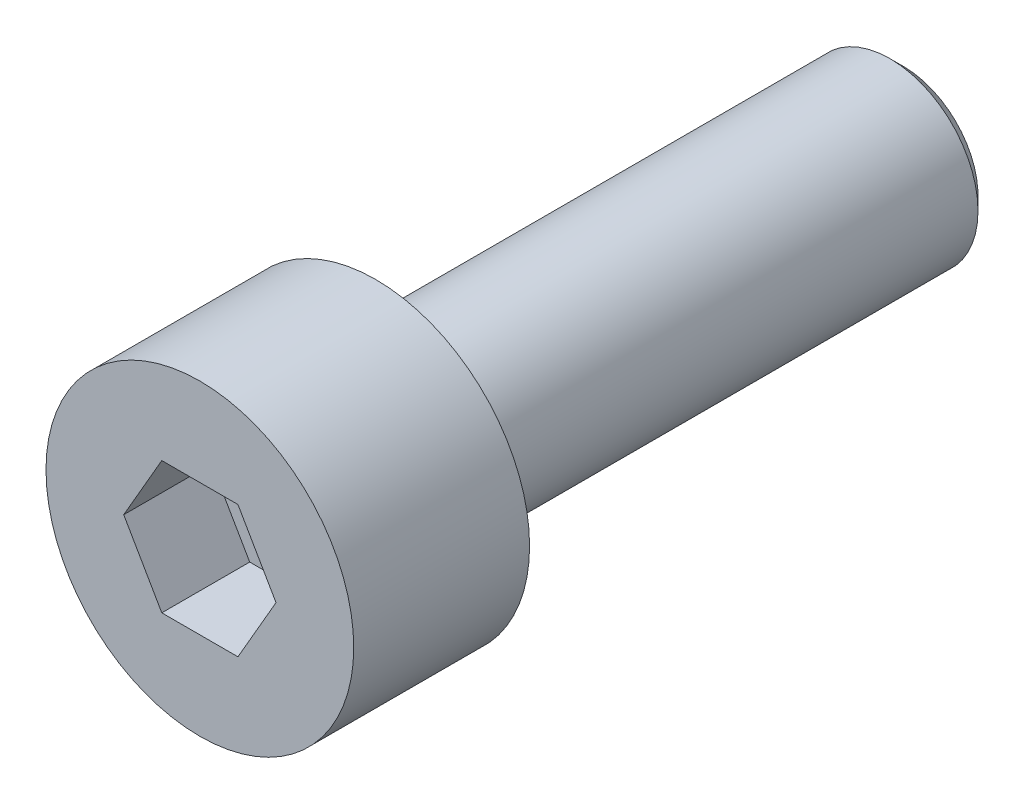
SolidWorks part; units mm, degrees
material "Простая углеродистая сталь"
ref_plane "Спереди" through (0, 0, 0) normal (0, 0, 1) x (1, 0, 0)
ref_plane "Сверху" through (0, 0, 0) normal (0, 1, 0) x (1, 0, 0)
ref_plane "Справа" through (0, 0, 0) normal (1, 0, 0) x (0, 0, -1)
sketch "Эскиз1" plane through (0, 0, 0) normal (1, 0, 0) x (0, 0, -1)
  line L0 (0, 0) -> (0, 3.5)
  line L1 (0, 3.5) -> (4, 3.5)
  line L2 (4, 3.5) -> (4, 2)
  line L3 (4, 2) -> (16, 2)
  line L4 (16, 2) -> (16, 0)
  line L5 (16, 0) -> (0, 0)
  line L6 (0, 0) -> (-1.7761, 0) construction
  dimension "D1" = 7
  dimension "D2" = 4
  dimension "D3" = 12
  dimension "D4" = 4
revolve "Повернуть1" add sketch "Эскиз1" angle 360 about L6
sketch "Эскиз2" plane through (0, 0, 0) normal (0, 0, 1) x (1, 0, 0)
  line L0 (0, 0) -> (0.8127, 0) construction
  line L1 (1.7321, 0) -> (0.866, 1.5)
  line L2 (0.866, 1.5) -> (-0.866, 1.5)
  line L3 (-0.866, 1.5) -> (-1.7321, 0)
  line L4 (-1.7321, 0) -> (-0.866, -1.5)
  line L5 (-0.866, -1.5) -> (0.866, -1.5)
  line L6 (0.866, -1.5) -> (1.7321, 0)
  circle A0 centre (0, 0) radius 1.5 construction
  dimension "D1" = 3
  dimension "D2" = 60
extrude "Вырез-Вытянуть1" cut sketch "Эскиз2" against normal blind 2
fillet "Скругление1" radius 0.3 1 edges at (-2, 0, -4)
chamfer "Фаска1" distance 0.3 angle 45 1 edges at (-2, 0, -16)
